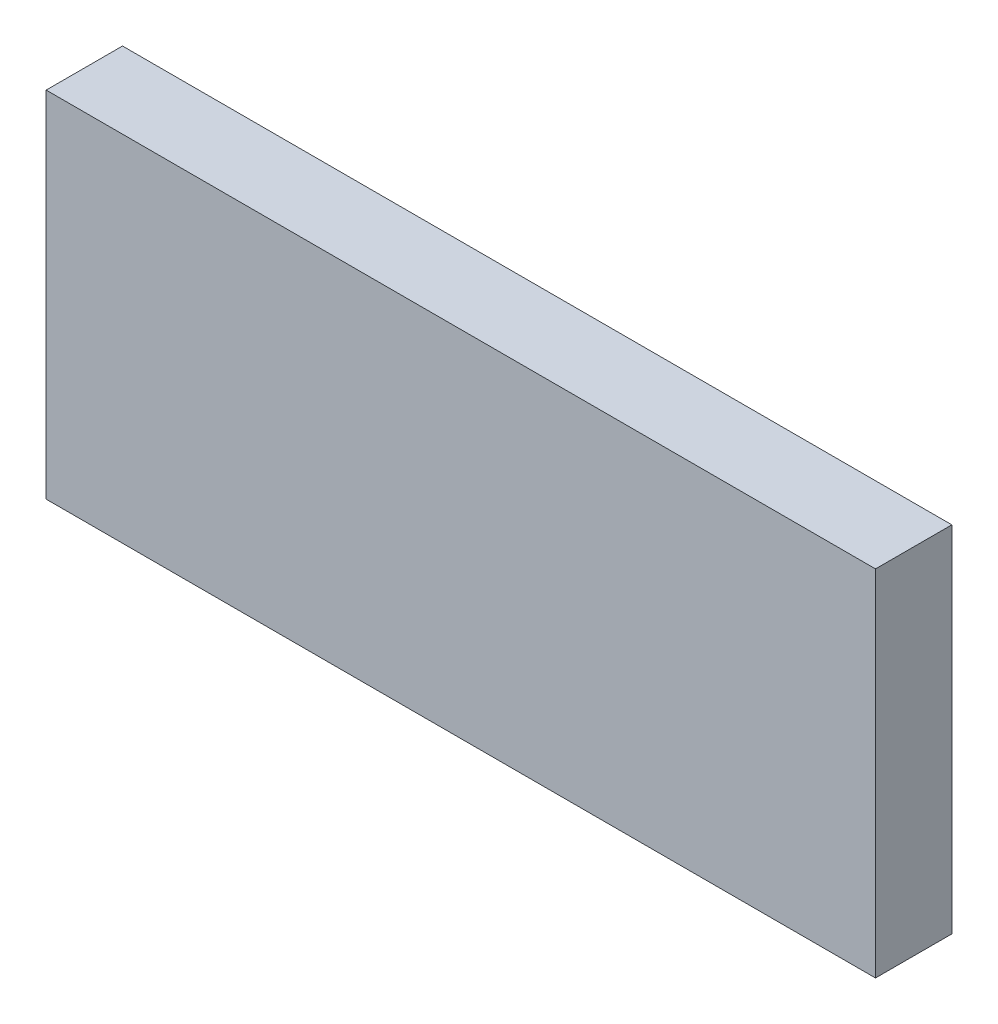
SolidWorks part; units mm, degrees
ref_plane "Plan de face" through (0, 0, 0) normal (0, 0, 1) x (1, 0, 0)
ref_plane "Plan de dessus" through (0, 0, 0) normal (0, 1, 0) x (1, 0, 0)
ref_plane "Plan de droite" through (0, 0, 0) normal (1, 0, 0) x (0, 0, -1)
sketch "Esquisse1" plane through (0, 0, 0) normal (0, 0, 1) x (1, 0, 0)
  line L1 (-36.702, 21.4105) -> (26.488, 21.4105)
  line L2 (-36.702, 21.4105) -> (-36.702, -6.4395)
  line L3 (-36.702, -6.4395) -> (26.488, -6.4395)
  line L4 (26.488, 21.4105) -> (26.488, -6.4395)
  dimension "D1" = 63.19
  dimension "D2" = 27.85
extrude "Boss.-Extru.1" add sketch "Esquisse1" along normal blind 6
sketch "Esquisse2" plane through (26.488, 0, 0) normal (1, 0, 0) x (0, 0, -1)
  line L1 (-6, -6.4395) -> (0, -6.4395)
  line L2 (-6, -6.4395) -> (-6, 21.4105)
  line L3 (-6, 21.4105) -> (0, 21.4105)
  line L4 (0, -6.4395) -> (0, 21.4105)
extrude "Boss.-Extru.2" add sketch "Esquisse2" along normal blind 2
